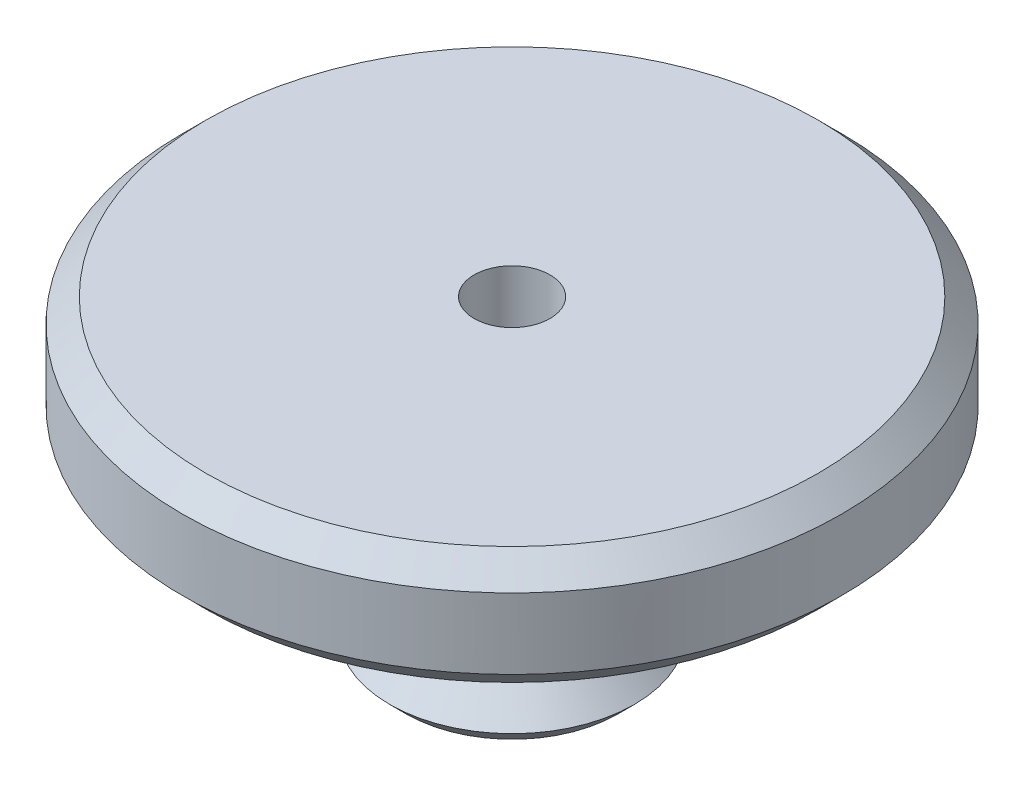
SolidWorks part; units mm, degrees
material "Сталь"
ref_plane "Спереди" through (0, 0, 0) normal (0, 0, 1) x (1, 0, 0)
ref_plane "Сверху" through (0, 0, 0) normal (0, 1, 0) x (1, 0, 0)
ref_plane "Справа" through (0, 0, 0) normal (1, 0, 0) x (0, 0, -1)
sketch "Эскиз1" plane through (0, 0, 0) normal (0, 0, 1) x (1, 0, 0)
  line L0 (0, 0) -> (14, 0)
  line L1 (14, 0) -> (14, -5)
  line L2 (14, -5) -> (5, -5)
  line L3 (5, -5) -> (5, -10)
  line L4 (5, -10) -> (4, -10)
  line L5 (4, -10) -> (4, -11.2)
  line L6 (4, -11.2) -> (5.2, -12.4)
  line L7 (5.2, -12.4) -> (4.4929, -13.1071)
  line L8 (4.4929, -13.1071) -> (2.5858, -11.2)
  line L9 (2.5858, -11.2) -> (2.5858, -10)
  line L10 (2.5858, -10) -> (0, -10)
  line L11 (0, -10) -> (0, 0)
  dimension "D1" = 14
  dimension "D2" = 5
  dimension "D3" = 5
  dimension "D4" = 4
  dimension "D5" = 1
  dimension "D6" = 135
  dimension "D7" = 5
  dimension "D8" = 1.2
  dimension "D9" = 1.2
revolve "Повернуть1" add sketch "Эскиз1" angle 360 about L11
sketch "Эскиз2" plane through (0, 0, 0) normal (0, 1, 0) x (1, 0, 0)
  circle A0 centre (0, 0) radius 1.61
  dimension "D1" = 3.22
extrude "Вырез-Вытянуть1" cut sketch "Эскиз2" against normal through all
cosmetic thread "Условное изображение резьбы1" parameters "D2"=4
chamfer "Фаска1" distance 0.39 angle 45 1 edges at (0, -10, -1.61)
chamfer "Фаска2" distance 1 angle 45 2 edges at (0, -5, -14) (0, 0, -14)
